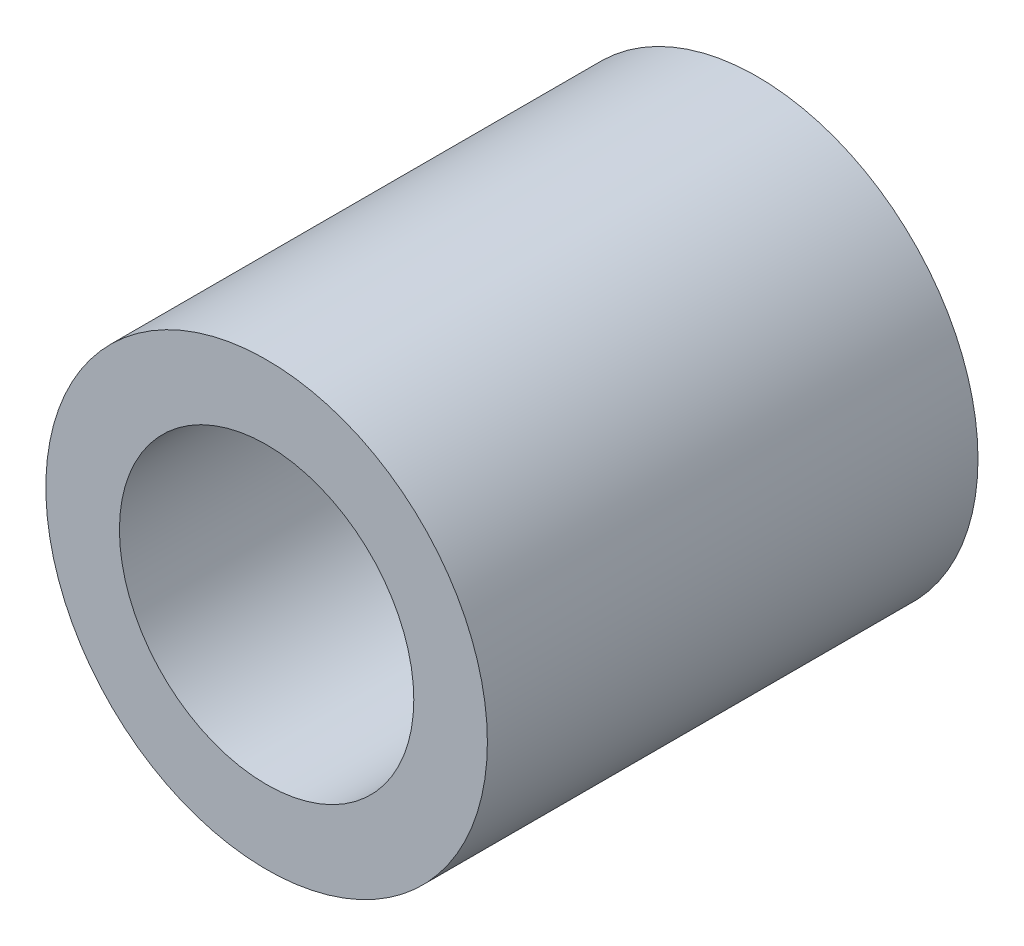
SolidWorks part; units mm, degrees
material "Tin Bearing Bronze"
ref_plane "Front Plane" through (0, 0, 0) normal (0, 0, 1) x (1, 0, 0)
ref_plane "Top Plane" through (0, 0, 0) normal (0, 1, 0) x (1, 0, 0)
ref_plane "Right Plane" through (0, 0, 0) normal (1, 0, 0) x (0, 0, -1)
sketch "Sketch1" plane through (0, 0, 0) normal (0, 0, 1) x (1, 0, 0)
  circle A0 centre (0, 0) radius 2.25
  circle A1 centre (0, 0) radius 1.5
  dimension "D1" = 3
  dimension "D2" = 4.5
extrude "Boss-Extrude1" add sketch "Sketch1" along normal mid plane 5
